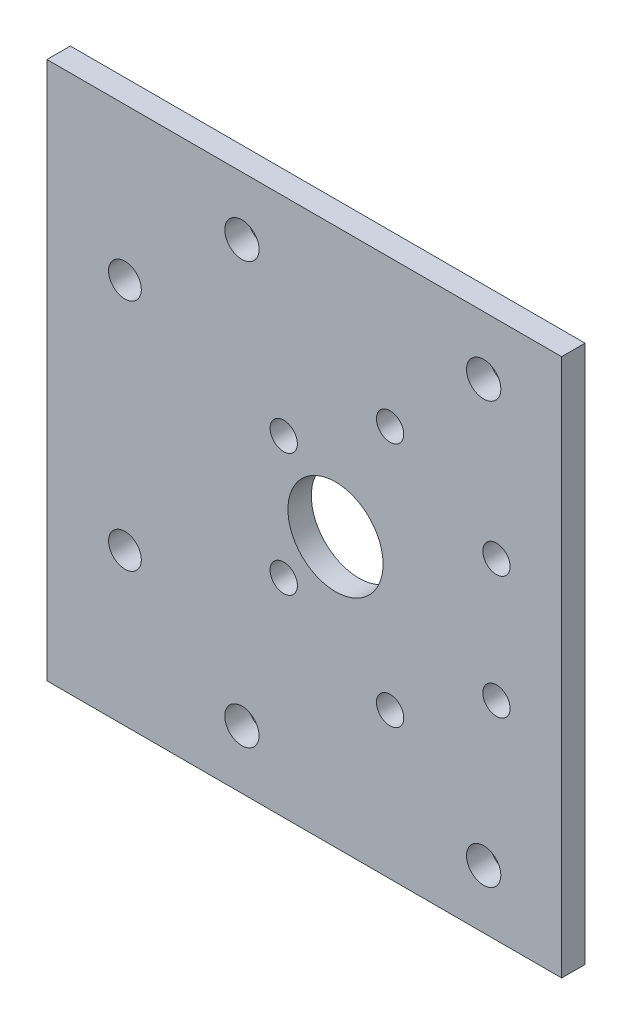
SolidWorks part; units mm, degrees
ref_plane "正面" through (0, 0, 0) normal (0, 0, 1) x (1, 0, 0)
ref_plane "平面" through (0, 0, 0) normal (0, 1, 0) x (1, 0, 0)
ref_plane "右側面" through (0, 0, 0) normal (1, 0, 0) x (0, 0, -1)
sketch "ｽｹｯﾁ1" plane through (0, 0, 0) normal (0, 0, 1) x (1, 0, 0)
  line L1 (-20, 14.5) -> (20, 14.5)
  line L2 (-20, 14.5) -> (-20, -14.5)
  line L3 (-20, -14.5) -> (20, -14.5)
  line L4 (20, 14.5) -> (20, -14.5)
  line L5 (-20, 14.5) -> (20, -14.5) construction
  line L6 (-20, -14.5) -> (20, 14.5) construction
  point P0 (0, 0)
  dimension "D1" = 40
  dimension "D2" = 29
extrude "ﾎﾞｽ - 押し出し1" add sketch "ｽｹｯﾁ1" along normal blind 3
sketch "ｽｹｯﾁ2" plane through (0, 0, 3) normal (0, 0, 1) x (1, 0, 0)
  line L1 (-20, 14.5) -> (-16.5, 14.5)
  line L2 (-20, 14.5) -> (-20, 10.5)
  line L3 (-20, 10.5) -> (-16.5, 10.5)
  line L4 (-16.5, 14.5) -> (-16.5, 10.5)
  line L5 (-20, -14.5) -> (-16.5, -14.5)
  line L6 (-20, -14.5) -> (-20, -10.5)
  line L7 (-20, -10.5) -> (-16.5, -10.5)
  line L8 (-16.5, -14.5) -> (-16.5, -10.5)
  line L9 (20, -14.5) -> (16.5, -14.5)
  line L10 (20, -14.5) -> (20, -10.5)
  line L11 (20, -10.5) -> (16.5, -10.5)
  line L12 (16.5, -14.5) -> (16.5, -10.5)
  line L13 (20, 14.5) -> (16.5, 14.5)
  line L14 (20, 14.5) -> (20, 10.5)
  line L15 (20, 10.5) -> (16.5, 10.5)
  line L16 (16.5, 14.5) -> (16.5, 10.5)
  circle A0 centre (-16.5, 10.5) radius 2.1
  circle A1 centre (-16.5, -10.5) radius 2.1
  circle A2 centre (16.5, -10.5) radius 2.1
  circle A3 centre (16.5, 10.5) radius 2.1
  dimension "D9" = 4.2
  dimension "D10" = 4.2
  dimension "D11" = 4.2
  dimension "D12" = 4.2
  dimension "D1" = 3.5
  dimension "D2" = 4
  dimension "D3" = 3.5
  dimension "D4" = 4
  dimension "D5" = 3.5
  dimension "D6" = 4
  dimension "D7" = 3.5
  dimension "D8" = 4
sketch "ｽｹｯﾁ3" plane through (0, -14.5, 0) normal (0, -1, 0) x (1, 0, 0)
  line L1 (20, 0) -> (-20, 0)
  line L2 (20, 0) -> (20, 3)
  line L3 (20, 3) -> (-20, 3)
  line L4 (-20, 0) -> (-20, 3)
extrude "ﾎﾞｽ - 押し出し2" add sketch "ｽｹｯﾁ3" along normal blind 10
sketch "ｽｹｯﾁ4" plane through (0, 14.5, 0) normal (0, 1, 0) x (1, 0, 0)
  line L1 (20, -3) -> (-20, -3)
  line L2 (20, -3) -> (20, 0)
  line L3 (20, 0) -> (-20, 0)
  line L4 (-20, -3) -> (-20, 0)
extrude "ﾎﾞｽ - 押し出し3" add sketch "ｽｹｯﾁ4" along normal blind 10
sketch "ｽｹｯﾁ6" plane through (20, 0, 0) normal (1, 0, 0) x (0, 0, -1)
  line L1 (0, 24.5) -> (-3, 24.5)
  line L2 (0, 24.5) -> (0, -24.5)
  line L3 (0, -24.5) -> (-3, -24.5)
  line L4 (-3, 24.5) -> (-3, -24.5)
extrude "ﾎﾞｽ - 押し出し5" add sketch "ｽｹｯﾁ6" along normal blind 42
sketch "ｽｹｯﾁ7" plane through (0, 0, 3) normal (0, 0, 1) x (1, 0, 0)
  line L0 (62, 0) -> (22, 0)
  line L1 (62, 24.5) -> (62, -24.5) construction
  line L2 (22, 0) -> (15, 0)
  line L7 (10.8631, -11.1369) -> (33.1369, 11.1369) construction
  line L8 (10.8631, 11.1369) -> (33.1369, -11.1369) construction
  line L9 (22, 0) -> (8.3601, 7.875)
  line L10 (22, 0) -> (22, 15.75)
  line L11 (22, 0) -> (35.6399, 7.875)
  line L12 (22, 0) -> (8.3601, -7.875)
  line L13 (22, 0) -> (22, -15.75)
  line L14 (22, 0) -> (35.6399, -7.875)
  circle A0 centre (22, 0) radius 15.75
  circle A5 centre (8.3601, 7.875) radius 1.75
  circle A6 centre (22, 15.75) radius 1.75
  circle A7 centre (8.3601, -7.875) radius 1.75
  circle A8 centre (22, -15.75) radius 1.75
  circle A9 centre (35.6399, -7.875) radius 1.75
  circle A10 centre (35.6399, 7.875) radius 1.75
  circle A11 centre (15, 0) radius 6.1
  dimension "D3" = 60
  dimension "D4" = 7
  dimension "D5" = 60
  dimension "D6" = 60
  dimension "D7" = 31.5
  dimension "D8" = 3.5
  dimension "D9" = 3.5
  dimension "D10" = 3.5
  dimension "D11" = 3.5
  dimension "D12" = 3.5
  dimension "D13" = 3.5
  dimension "D14" = 12.2
  dimension "D2" = 60
  dimension "D15" = 40
sketch "ｽｹｯﾁ8" plane through (-20, 0, 0) normal (-1, 0, 0) x (0, 0, 1)
  line L1 (3, -24.5) -> (0, -24.5)
  line L2 (3, -24.5) -> (3, 24.5)
  line L3 (3, 24.5) -> (0, 24.5)
  line L4 (0, -24.5) -> (0, 24.5)
extrude "ﾎﾞｽ - 押し出し6" add sketch "ｽｹｯﾁ8" along normal blind 2
sketch "ｽｹｯﾁ9" plane through (62, 0, 0) normal (1, 0, 0) x (0, 0, -1)
  line L1 (0, 24.5) -> (-3, 24.5)
  line L2 (0, 24.5) -> (0, -24.5)
  line L3 (0, -24.5) -> (-3, -24.5)
  line L4 (-3, 24.5) -> (-3, -24.5)
extrude "ﾎﾞｽ - 押し出し7" add sketch "ｽｹｯﾁ9" along normal blind 2
sketch "ｽｹｯﾁ10" plane through (0, -24.5, 0) normal (0, -1, 0) x (1, 0, 0)
  line L1 (-22, 0) -> (64, 0)
  line L2 (-22, 0) -> (-22, 3)
  line L3 (-22, 3) -> (64, 3)
  line L4 (64, 0) -> (64, 3)
extrude "ﾎﾞｽ - 押し出し8" add sketch "ｽｹｯﾁ10" along normal blind 10
sketch "ｽｹｯﾁ11" plane through (0, 24.5, 0) normal (0, 1, 0) x (1, 0, 0)
  line L1 (-22, 0) -> (64, 0)
  line L2 (-22, 0) -> (-22, -3)
  line L3 (-22, -3) -> (64, -3)
  line L4 (64, 0) -> (64, -3)
extrude "ﾎﾞｽ - 押し出し9" add sketch "ｽｹｯﾁ11" along normal blind 10
sketch "ｽｹｯﾁ12" plane through (0, 0, 3) normal (0, 0, 1) x (1, 0, 0)
  line L0 (64, -34.5) -> (64, -27)
  line L1 (64, 34.5) -> (64, -34.5) construction
  line L2 (64, 34.5) -> (64, 27)
  line L3 (64, -27) -> (34, -27)
  line L4 (64, 27) -> (34, 27)
  line L5 (-22, -34.5) -> (-22, -27)
  line L6 (-22, -34.5) -> (-22, 34.5) construction
  line L7 (-22, 34.5) -> (-22, 27)
  line L8 (-22, -27) -> (3, -27)
  line L9 (-22, 27) -> (3, 27)
  circle A0 centre (34, -27) radius 2.2
  circle A1 centre (34, 27) radius 2.2
  circle A2 centre (3, -27) radius 2.2
  circle A3 centre (3, 27) radius 2.2
  dimension "D4" = 4.4
  dimension "D5" = 4.4
  dimension "D11" = 4.4
  dimension "D12" = 4.4
  dimension "D1" = 7.5
  dimension "D2" = 7.5
  dimension "D3" = 30
  dimension "D6" = 30
  dimension "D7" = 7.5
  dimension "D8" = 7.5
  dimension "D9" = 25
  dimension "D10" = 25
extrude "ｶｯﾄ - 押し出し3" cut sketch "ｽｹｯﾁ12" against normal blind 7.5
extrude "ｶｯﾄ - 押し出し4" cut sketch "ｽｹｯﾁ7" against normal blind 10
sketch "ｽｹｯﾁ13" plane through (0, 0, 3) normal (0, 0, 1) x (1, 0, 0)
  line L0 (-22, 0) -> (-12, 0)
  line L1 (-22, -34.5) -> (-22, 34.5) construction
  line L2 (-12, 0) -> (-12, 15)
  line L3 (-12, 0) -> (-12, -15)
  circle A0 centre (-12, -15) radius 2.1
  circle A1 centre (-12, 15) radius 2.1
  dimension "D4" = 4.2
  dimension "D5" = 4.2
  dimension "D1" = 10
  dimension "D2" = 15
  dimension "D3" = 15
extrude "ｶｯﾄ - 押し出し5" cut sketch "ｽｹｯﾁ13" against normal blind 10
sketch "ｽｹｯﾁ14" plane through (64, 0, 0) normal (1, 0, 0) x (0, 0, -1)
  line L0 (0, -34.5) -> (0, 34.5) construction
  line L1 (-3, -34.5) -> (0, -34.5)
  line L2 (-3, -34.5) -> (-3, 34.5)
  line L3 (-3, 34.5) -> (0, 34.5)
  line L4 (0, -34.5) -> (0, 34.5)
extrude "ｶｯﾄ - 押し出し6" cut sketch "ｽｹｯﾁ14" against normal blind 20
